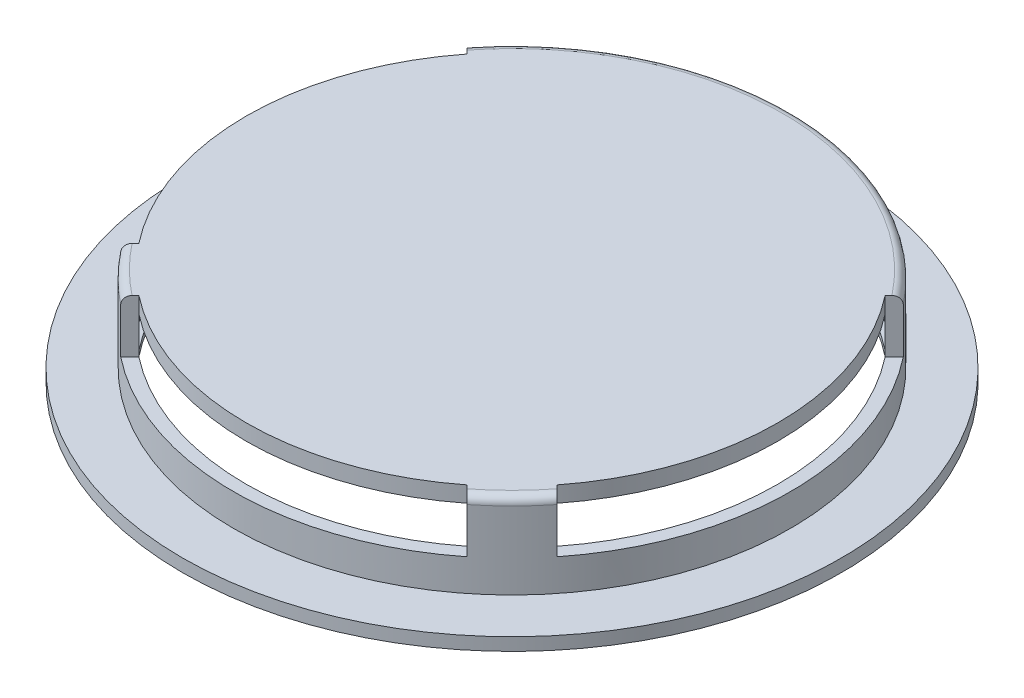
SolidWorks part; units mm, degrees
material "ABS"
ref_plane "Front Plane" through (0, 0, 0) normal (0, 0, 1) x (1, 0, 0)
ref_plane "Top Plane" through (0, 0, 0) normal (0, 1, 0) x (1, 0, 0)
ref_plane "Right Plane" through (0, 0, 0) normal (1, 0, 0) x (0, 0, -1)
sketch "Sketch1" plane through (0, 0, 0) normal (0, 1, 0) x (1, 0, 0)
  circle A0 centre (0, 0) radius 31
  circle A1 centre (0, 0) radius 25
  dimension "D1" = 62
  dimension "D2" = 50
extrude "Boss-Extrude1" add sketch "Sketch1" along normal blind 1.2
sketch "Sketch2" plane through (0, 1.2, 0) normal (0, 1, 0) x (1, 0, 0)
  circle A0 centre (0, 0) radius 25 construction
  circle A1 centre (0, 0) radius 25
  circle A2 centre (0, 0) radius 26.2
  dimension "D1" = 1.2
extrude "Boss-Extrude2" add sketch "Sketch2" along normal blind 6.5
sketch "Sketch3" plane through (0, 7.7, 0) normal (0, 1, 0) x (1, 0, 0)
  circle A0 centre (0, 0) radius 26.2 construction
  circle A1 centre (0, 0) radius 26.2
extrude "Boss-Extrude3" add sketch "Sketch3" along normal blind 1.5
sketch "Sketch5" plane through (0, 9.2, 0) normal (0, 1, 0) x (1, 0, 0)
  line L0 (-18.5262, -18.5262) -> (18.5262, 18.5262) construction
  line L1 (18.5262, -18.5262) -> (-18.5262, 18.5262) construction
  line L2 (0, 0) -> (0, 26.2) construction
  line L3 (20.5257, 16.283) -> (19.6712, 15.4286)
  line L4 (16.283, -20.5257) -> (15.4286, -19.6712)
  line L6 (20.5257, -16.283) -> (19.6712, -15.4286)
  line L7 (-15.4286, -19.6712) -> (-16.283, -20.5257)
  line L17 (-19.6712, -15.4286) -> (-20.5257, -16.283)
  line L19 (-19.6712, 15.4286) -> (-20.5257, 16.283)
  arc A0 (-15.4286, -19.6712) -> (15.4286, -19.6712) centre (0, 0) ccw
  circle A1 centre (0, 0) radius 26.2 construction
  arc A2 (-16.283, -20.5257) -> (16.283, -20.5257) centre (0, 0) ccw
  arc A3 (20.5257, -16.283) -> (20.5257, 16.283) centre (0, 0) ccw
  arc A4 (19.6712, -15.4286) -> (19.6712, 15.4286) centre (0, 0) ccw
  arc A5 (-19.6712, 15.4286) -> (-19.6712, -15.4286) centre (0, 0) ccw
  arc A6 (-20.5257, 16.283) -> (-20.5257, -16.283) centre (0, 0) ccw
  circle A7 centre (0, 0) radius 26.2 construction
  point P9 (0, 0)
  point P12 (0, 0)
  point P15 (0, 0)
  point P19 (0, 0)
  dimension "D1" = 1.2
  dimension "D2" = 6
  dimension "D3" = 6
  dimension "D4" = 45
  dimension "D5" = 90
  dimension "D6" = 3
  dimension "D7" = 3
extrude "Cut-Extrude2" cut sketch "Sketch5" against normal blind 5
sketch "Sketch7" plane through (0, 0, 0) normal (0, -1, 0) x (1, 0, 0)
  circle A0 centre (0, 0) radius 25.6
  circle A1 centre (0, 0) radius 25 construction
  circle A2 centre (0, 0) radius 25
  dimension "D1" = 0.6
extrude "Cut-Extrude3" cut sketch "Sketch7" against normal blind 3 from offset 0.5 offset against normal yes
fillet "Fillet1" radius 0.75 3 edges at (18.5262, 9.2, 18.5262) (-18.5262, 9.2, 18.5262) (0, 9.2, -26.2)
sketch "Sketch8" plane through (0, 7.7, 0) normal (0, -1, 0) x (1, 0, 0)
  circle A0 centre (0, 0) radius 3.5
  circle A1 centre (0, 0) radius 2
  dimension "D1" = 4
  dimension "D2" = 1.5
extrude "Boss-Extrude4" add sketch "Sketch8" along normal blind 3.5
